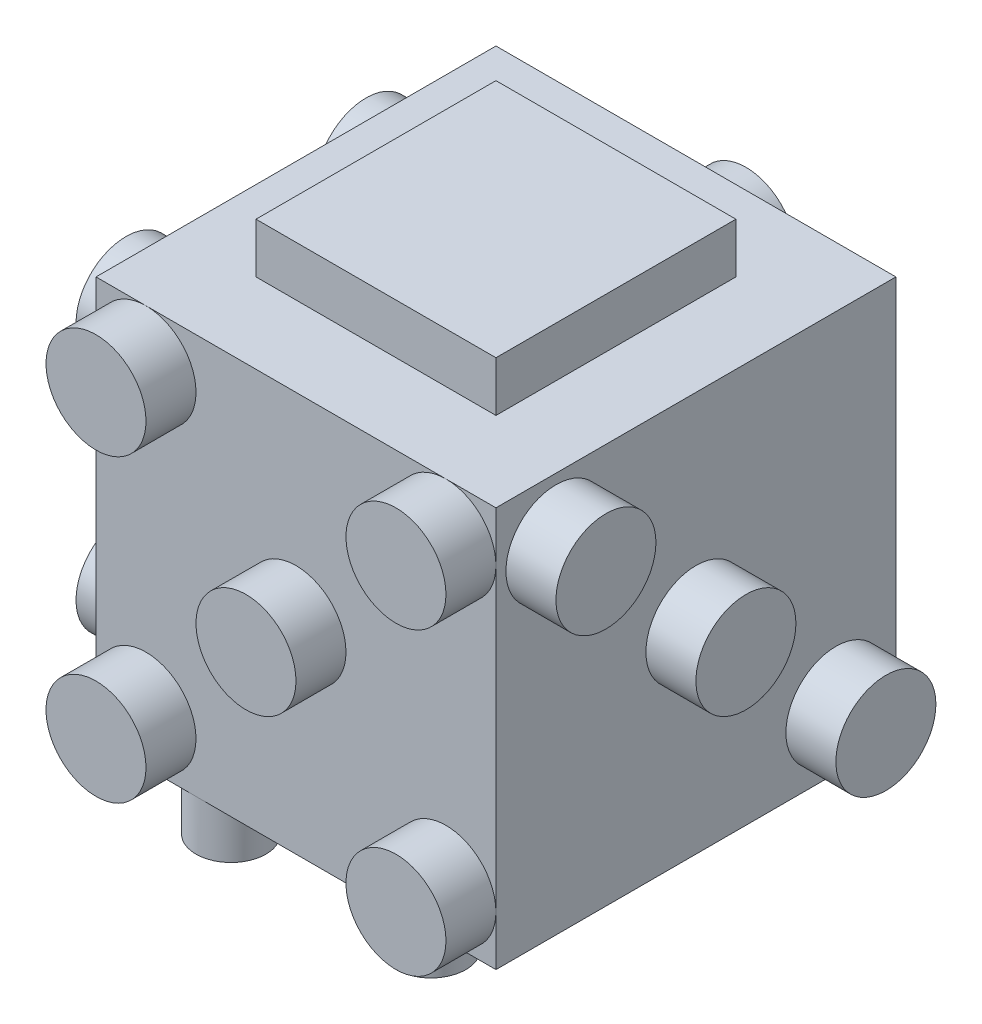
SolidWorks part; units mm, degrees
ref_plane "Front Plane" through (0, 0, 0) normal (0, 0, 1) x (1, 0, 0)
ref_plane "Top Plane" through (0, 0, 0) normal (0, 1, 0) x (1, 0, 0)
ref_plane "Right Plane" through (0, 0, 0) normal (1, 0, 0) x (0, 0, -1)
sketch "Sketch1" plane through (0, 0, 0) normal (0, 1, 0) x (1, 0, 0)
  line L1 (-12.5, 12.5) -> (12.5, 12.5)
  line L2 (-12.5, 12.5) -> (-12.5, -12.5)
  line L3 (-12.5, -12.5) -> (12.5, -12.5)
  line L4 (12.5, 12.5) -> (12.5, -12.5)
  line L5 (0, -12.5) -> (0, 12.5) construction
  line L6 (-12.5, 0) -> (12.5, 0) construction
  point P0 (0, 0)
  dimension "D1" = 25
  dimension "D2" = 25
extrude "Boss-Extrude1" add sketch "Sketch1" along normal blind 25
sketch "Sketch2" plane through (0, 25, 0) normal (0, 1, 0) x (1, 0, 0)
  line L1 (-6, 6) -> (6, 6)
  line L2 (-6, 6) -> (-6, -6)
  line L3 (-6, -6) -> (6, -6)
  line L4 (6, 6) -> (6, -6)
  line L5 (0, -6) -> (0, 6) construction
  line L6 (-6, 0) -> (6, 0) construction
  point P0 (0, 0)
  dimension "D1" = 12
  dimension "D2" = 12
sketch "Sketch3" plane through (0, 0, 0) normal (0, -1, 0) x (1, 0, 0)
  line L1 (10, 10) -> (-10, 10) construction
  line L2 (10, 10) -> (10, -10) construction
  line L3 (10, -10) -> (-10, -10) construction
  line L4 (-10, 10) -> (-10, -10) construction
  line L5 (0, -10) -> (0, 10) construction
  line L6 (10, 0) -> (-10, 0) construction
  line L7 (5, -8.25) -> (-5, -8.25) construction
  line L8 (5, -8.25) -> (5, 8.25) construction
  line L9 (5, 8.25) -> (-5, 8.25) construction
  line L10 (-5, -8.25) -> (-5, 8.25) construction
  line L11 (0, 8.25) -> (0, -8.25) construction
  line L12 (5, 0) -> (-5, 0) construction
  circle A0 centre (-5, 8.25) radius 1.75
  circle A1 centre (-5, 0) radius 1.75
  circle A2 centre (-5, -8.25) radius 1.75
  circle A3 centre (5, 8.25) radius 1.75
  circle A4 centre (5, 0) radius 1.75
  circle A5 centre (5, -8.25) radius 1.75
  point P0 (0, 0)
  point P4 (0, 0)
  point P14 (5, 1.75)
  point P15 (5, 6.5)
  dimension "D5" = 3.5
  dimension "D6" = 3.5
  dimension "D7" = 3.5
  dimension "D8" = 3.5
  dimension "D9" = 3.5
  dimension "D10" = 3.5
  dimension "D1" = 20
  dimension "D2" = 20
  dimension "D3" = 10
  dimension "D4" = 16.5
sketch "Sketch4" plane through (12.5, 0, 0) normal (1, 0, 0) x (0, 0, -1)
  line L0 (-7, 19.5) -> (-7, 25) construction
  line L1 (-7, 19.5) -> (-12.5, 19.5) construction
  line L4 (-12.5, 0) -> (12.5, 0)
  line L5 (12.5, 0) -> (12.5, 25)
  line L6 (12.5, 25) -> (-12.5, 25)
  line L7 (-12.5, 25) -> (-12.5, 0)
  line L8 (-12.5, 0) -> (12.5, 0)
  line L10 (12.5, 25) -> (-12.5, 25)
  line L11 (-12.5, 25) -> (-12.5, 0)
  line L13 (7, 5.5) -> (7, 0) construction
  line L14 (7, 5.5) -> (12.5, 5.5) construction
  line L15 (12.5, 25) -> (12.5, 0) construction
  line L16 (0, 12.5) -> (0, 25) construction
  circle A0 centre (-7, 19.5) radius 2.5
  circle A1 centre (0, 12.5) radius 2.5
  circle A2 centre (7, 5.5) radius 2.5
  point P2 (5.3399, 7.3693)
  point P17 (1.7263, 10.6917)
  dimension "D5" = 5
  dimension "D6" = 5
  dimension "D7" = 5
  dimension "D8" = 5.5
  dimension "D2" = 5.5
  dimension "D3" = 5.5
  dimension "D4" = 5.5
  dimension "D9" = 12.5
  dimension "D1" = 0
sketch "Sketch5" plane through (-12.5, 0, 0) normal (-1, 0, 0) x (0, 0, 1)
  line L0 (-12.5, 12.5) -> (0, 12.5) construction
  line L2 (-10, 22.5) -> (10, 22.5) construction
  line L3 (-10, 22.5) -> (-10, 2.5) construction
  line L4 (-12.5, 0) -> (12.5, 0)
  line L5 (12.5, 0) -> (12.5, 25)
  line L6 (12.5, 25) -> (-12.5, 25)
  line L7 (-12.5, 25) -> (-12.5, 0)
  line L8 (-12.5, 0) -> (12.5, 0)
  line L9 (12.5, 0) -> (12.5, 25)
  line L10 (12.5, 25) -> (-12.5, 25)
  line L11 (-12.5, 25) -> (-12.5, 0)
  line L12 (-10, 2.5) -> (10, 2.5) construction
  line L13 (10, 22.5) -> (10, 2.5) construction
  line L14 (0, 2.5) -> (0, 22.5) construction
  line L15 (-10, 12.5) -> (10, 12.5) construction
  line L16 (-6, 18.5) -> (6, 18.5) construction
  line L17 (-6, 18.5) -> (-6, 6.5) construction
  line L18 (-6, 6.5) -> (6, 6.5) construction
  line L19 (6, 18.5) -> (6, 6.5) construction
  line L20 (0, 6.5) -> (0, 18.5) construction
  line L21 (-6, 12.5) -> (6, 12.5) construction
  circle A0 centre (-6, 18.5) radius 2.5
  circle A1 centre (6, 18.5) radius 2.5
  circle A2 centre (6, 6.5) radius 2.5
  circle A3 centre (-6, 6.5) radius 2.5
  dimension "D6" = 5
  dimension "D7" = 5
  dimension "D8" = 5
  dimension "D9" = 5
  dimension "D2" = 20
  dimension "D3" = 20
  dimension "D4" = 12
  dimension "D5" = 12
  dimension "D1" = 0
sketch "Sketch7" plane through (0, 0, 12.5) normal (0, 0, 1) x (1, 0, 0)
  line L0 (0, 25) -> (0, 12.5) construction
  line L1 (0, 12.5) -> (7.5, 20) construction
  line L2 (-10, 22.5) -> (10, 22.5) construction
  line L3 (-10, 22.5) -> (-10, 2.5) construction
  line L4 (-12.5, 0) -> (12.5, 0)
  line L5 (12.5, 0) -> (12.5, 25)
  line L6 (12.5, 25) -> (-12.5, 25)
  line L7 (-12.5, 25) -> (-12.5, 0)
  line L8 (-12.5, 0) -> (12.5, 0)
  line L9 (12.5, 0) -> (12.5, 25)
  line L10 (12.5, 25) -> (-12.5, 25)
  line L11 (-12.5, 25) -> (-12.5, 0)
  line L12 (-10, 2.5) -> (10, 2.5) construction
  line L13 (10, 22.5) -> (10, 2.5) construction
  line L14 (0, 2.5) -> (0, 22.5) construction
  line L15 (-10, 12.5) -> (10, 12.5) construction
  line L16 (-7.5, 20) -> (7.5, 20) construction
  line L17 (-7.5, 20) -> (-7.5, 5) construction
  line L18 (-7.5, 5) -> (7.5, 5) construction
  line L19 (7.5, 20) -> (7.5, 5) construction
  line L20 (0, 5) -> (0, 20) construction
  line L21 (-7.5, 12.5) -> (7.5, 12.5) construction
  circle A0 centre (-7.5, 20) radius 2.5
  circle A1 centre (0, 12.5) radius 2.5
  circle A2 centre (7.5, 20) radius 2.5
  circle A3 centre (7.5, 5) radius 2.5
  circle A4 centre (-7.5, 5) radius 2.5
  point P18 (1.7678, 14.2678)
  point P19 (5.7322, 18.2322)
  dimension "D7" = 5
  dimension "D8" = 5
  dimension "D9" = 5
  dimension "D10" = 5
  dimension "D11" = 5
  dimension "D2" = 12.5
  dimension "D3" = 20
  dimension "D4" = 20
  dimension "D5" = 15
  dimension "D6" = 15
  dimension "D1" = 0
sketch "Sketch8" plane through (0, 0, -12.5) normal (0, 0, -1) x (-1, 0, 0)
  line L0 (0, 0) -> (0, 12.5) construction
  line L1 (10, 22.5) -> (-10, 2.5) construction
  line L2 (-10, 22.5) -> (10, 22.5) construction
  line L3 (-10, 22.5) -> (-10, 2.5) construction
  line L4 (-12.5, 0) -> (12.5, 0)
  line L5 (12.5, 0) -> (12.5, 25)
  line L6 (12.5, 25) -> (-12.5, 25)
  line L7 (-12.5, 25) -> (-12.5, 0)
  line L8 (-12.5, 0) -> (12.5, 0)
  line L9 (12.5, 0) -> (12.5, 25)
  line L10 (12.5, 25) -> (-12.5, 25)
  line L11 (-12.5, 25) -> (-12.5, 0)
  line L12 (-10, 2.5) -> (10, 2.5) construction
  line L13 (10, 22.5) -> (10, 2.5) construction
  line L14 (0, 2.5) -> (0, 22.5) construction
  line L15 (-10, 12.5) -> (10, 12.5) construction
  line L17 (-6, 18.5) -> (6, 18.5) construction
  line L18 (-6, 18.5) -> (-6, 6.5) construction
  line L19 (-6, 6.5) -> (6, 6.5) construction
  line L20 (6, 18.5) -> (6, 6.5) construction
  line L21 (0, 6.5) -> (0, 18.5) construction
  line L22 (-6, 12.5) -> (6, 12.5) construction
  circle A4 centre (0, 18.5) radius 2.5
  circle A5 centre (0, 6.5) radius 2.5
  dimension "D7" = 5
  dimension "D8" = 5
  dimension "D2" = 12.5
  dimension "D3" = 20
  dimension "D4" = 20
  dimension "D5" = 12
  dimension "D6" = 12
  dimension "D1" = 0
scale "Scale1" bodies to scale 111 scale about centroid uniform scaling yes scale factor 0.8
extrude "Boss-Extrude2" add sketch "Sketch3" against normal up to surface (2.5 mm away) separate body contours A2 | A1 | A0 | A5 | A4 | A3 up to face at (0, 2.5, 0)
extrude "Boss-Extrude3" add sketch "Sketch7" against normal up to surface (2.5 mm away) contours A0 | A2 | A1 | A4 | A3 up to face at (0, 12.5, 10)
extrude "Boss-Extrude4" add sketch "Sketch5" against normal up to surface (2.5 mm away) contours A3 | A2 | A1 | A0 up to face at (-10, 12.5, 3.3333)
extrude "Boss-Extrude5" add sketch "Sketch4" against normal up to surface (2.5 mm away) contours A2 | A1 | A0 up to face at (10, 12.5, 3.3333)
extrude "Boss-Extrude7" add sketch "Sketch2" against normal up to surface (2.5 mm away) contours L4 L3 L2 L1 up to face at (0, 22.5, 3.3333)
extrude "Boss-Extrude8" add sketch "Sketch8" against normal blind 10 contours A5 | A4
